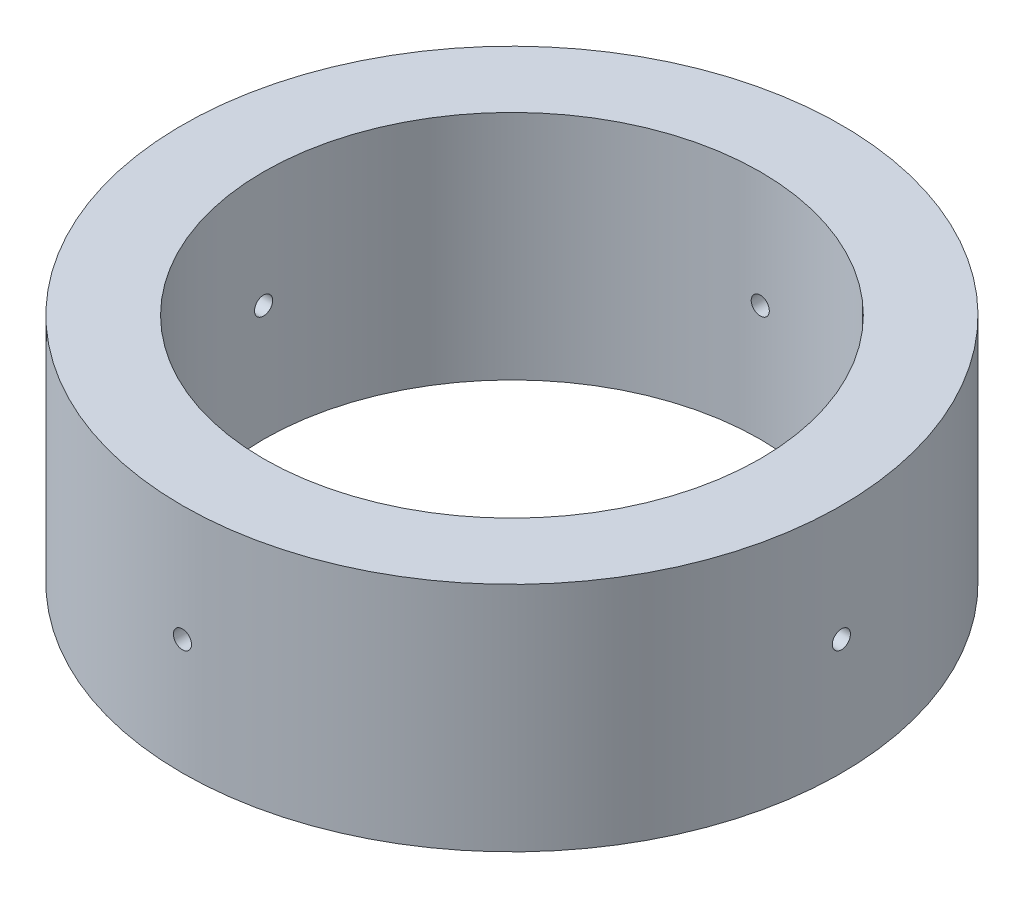
SolidWorks part; units mm, degrees
ref_plane "Front Plane" through (0, 0, 0) normal (0, 0, 1) x (1, 0, 0)
ref_plane "Top Plane" through (0, 0, 0) normal (0, 1, 0) x (1, 0, 0)
ref_plane "Right Plane" through (0, 0, 0) normal (1, 0, 0) x (0, 0, -1)
sketch "Sketch1" plane through (0, 0, 0) normal (0, 1, 0) x (1, 0, 0)
  circle A0 centre (0, 0) radius 27.2415
  circle A1 centre (0, 0) radius 36.1315
  dimension "D1" = 54.483
  dimension "D2" = 8.89
extrude "Boss-Extrude1" add sketch "Sketch1" along normal blind 25.4
ref_plane "Plane1" through (0, 0, 36.1315) normal (0, 0, 1) x (1, 0, 0)
sketch "Sketch2" plane through (0, 0, 36.1315) normal (0, 0, 1) x (1, 0, 0)
  line L0 (0, 0) -> (0, 25.4) construction
  line L1 (-36.1315, 0) -> (36.1315, 0) construction
  line L2 (36.1315, 25.4) -> (-36.1315, 25.4) construction
  circle A0 centre (0, 12.7) radius 0.9922
  point P2 (0, 7.4115)
  point P10 (0, 12.7)
  dimension "D1" = 1.9844
extrude "Cut-Extrude1" cut sketch "Sketch2" against normal up to next
pattern_circular "CirPattern1" count 4 over 360 about axis through (0, 25.4, 0) along (0, -1, 0) of "Cut-Extrude1"
